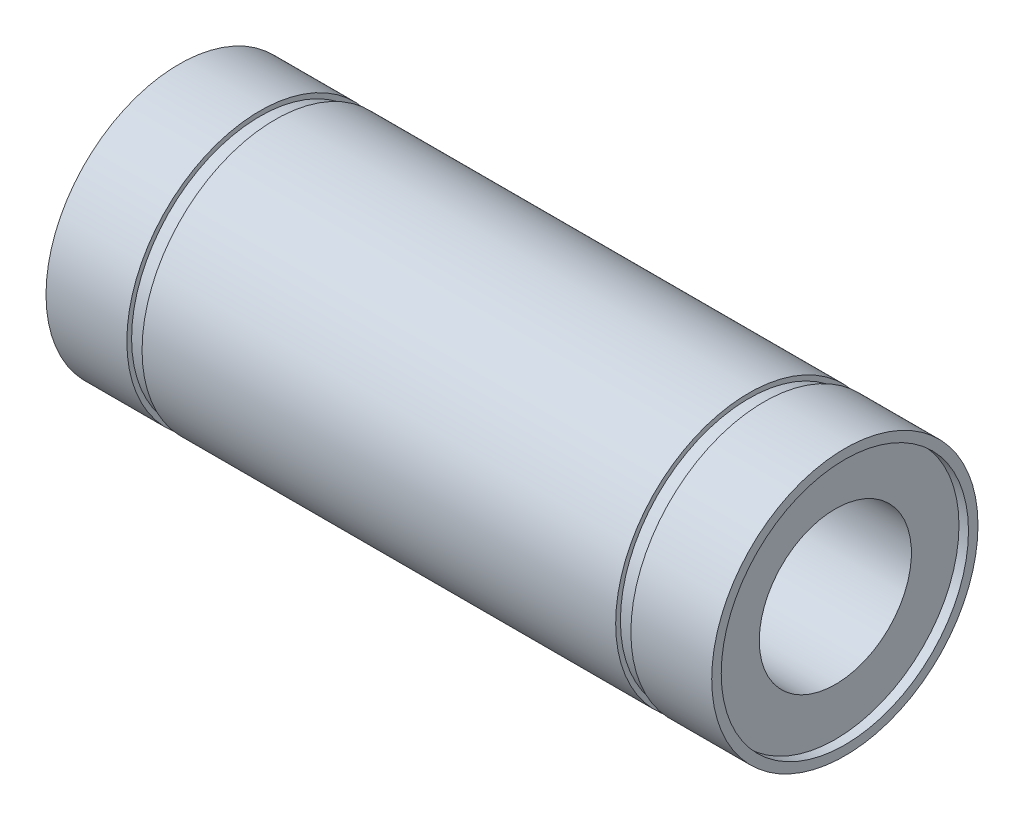
SolidWorks part; units mm, degrees
material "Stainless Steel (ferritic)"
ref_plane "Front Plane" through (0, 0, 0) normal (0, 0, 1) x (1, 0, 0)
ref_plane "Top Plane" through (0, 0, 0) normal (0, 1, 0) x (1, 0, 0)
ref_plane "Right Plane" through (0, 0, 0) normal (1, 0, 0) x (0, 0, -1)
sketch "Sketch1" plane through (0, 0, 0) normal (0, 0, 1) x (1, 0, 0)
  line L0 (24.9, 14) -> (24.9, 13.5)
  line L1 (-35, 0) -> (35, 0) construction
  line L2 (0, 0) -> (0, 14) construction
  line L3 (-35, 14) -> (-26.5, 14)
  line L4 (35, 13) -> (35, 14)
  line L5 (24.9, 13.5) -> (26.5, 13.5)
  line L6 (26.5, 13.5) -> (26.5, 14)
  line L7 (35, 13) -> (34, 13)
  line L8 (34, 13) -> (34, 8)
  line L9 (34, 8) -> (-34, 8)
  line L10 (-34, 13) -> (-34, 8)
  line L11 (-35, 13) -> (-34, 13)
  line L12 (-26.5, 13.5) -> (-26.5, 14)
  line L13 (-24.9, 13.5) -> (-26.5, 13.5)
  line L14 (-35, 13) -> (-35, 14)
  line L15 (-24.9, 14) -> (-24.9, 13.5)
  line L16 (-24.9, 14) -> (24.9, 14)
  line L17 (26.5, 14) -> (35, 14)
  point P15 (0, 8)
  dimension "D1" = 35
  dimension "D2" = 14
  dimension "D3" = 16
  dimension "D4" = 1
  dimension "D5" = 1
  dimension "D6" = 1.6
  dimension "D7" = 26.5
  dimension "D8" = 27
revolve "Revolve2" add sketch "Sketch1" angle 360 about L1
